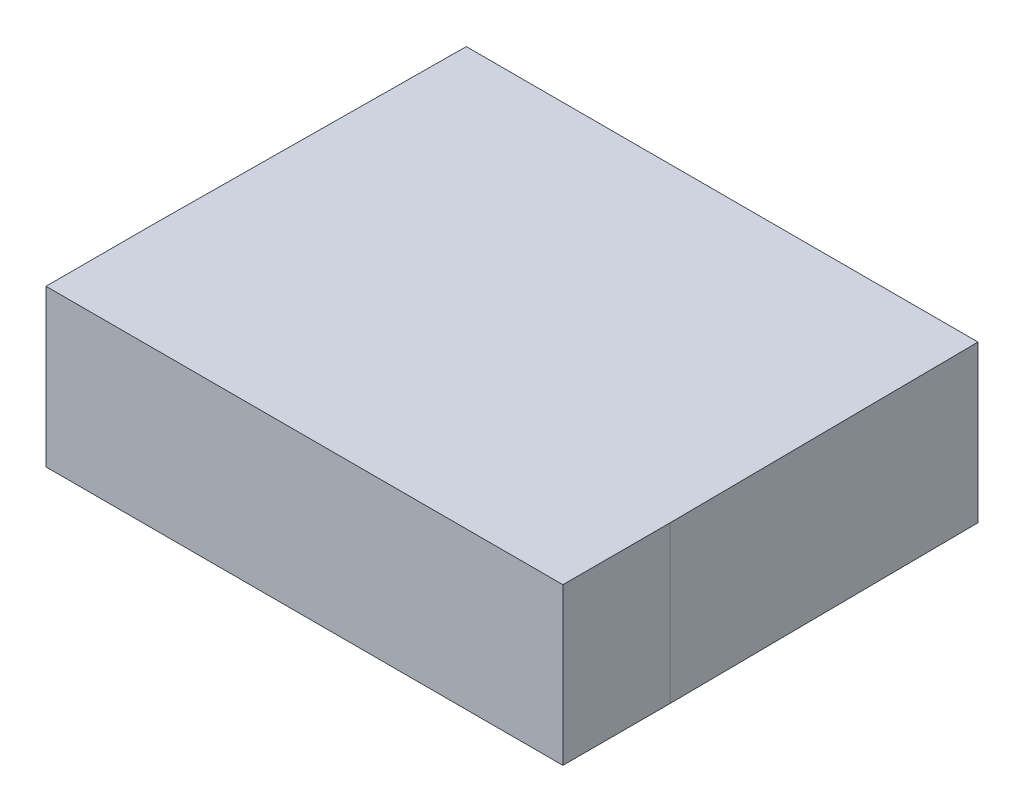
SolidWorks part; units mm, degrees
ref_plane "Front Plane" through (0, 0, 0) normal (0, 0, 1) x (1, 0, 0)
ref_plane "Top Plane" through (0, 0, 0) normal (0, 1, 0) x (1, 0, 0)
ref_plane "Right Plane" through (0, 0, 0) normal (1, 0, 0) x (0, 0, -1)
sketch "Sketch1" plane through (0, 0, 0) normal (0, 1, 0) x (1, 0, 0)
  line L0 (-4.9, 0) -> (4.9, 0)
  line L1 (4.9, 0) -> (4.95, -5.95)
  line L2 (4.95, -5.95) -> (4.95, -8)
  line L3 (4.95, -8) -> (-4.95, -8)
  line L4 (-4.95, -8) -> (-4.95, -5.95)
  line L5 (-4.95, -5.95) -> (-4.9, 0)
  point P9 (0, -8)
  point P10 (0, 0)
  dimension "D1" = 9.8
  dimension "D2" = 9.9
  dimension "D3" = 5.95
  dimension "D4" = 8
extrude "Boss-Extrude1" add sketch "Sketch1" along normal blind 2.9972
